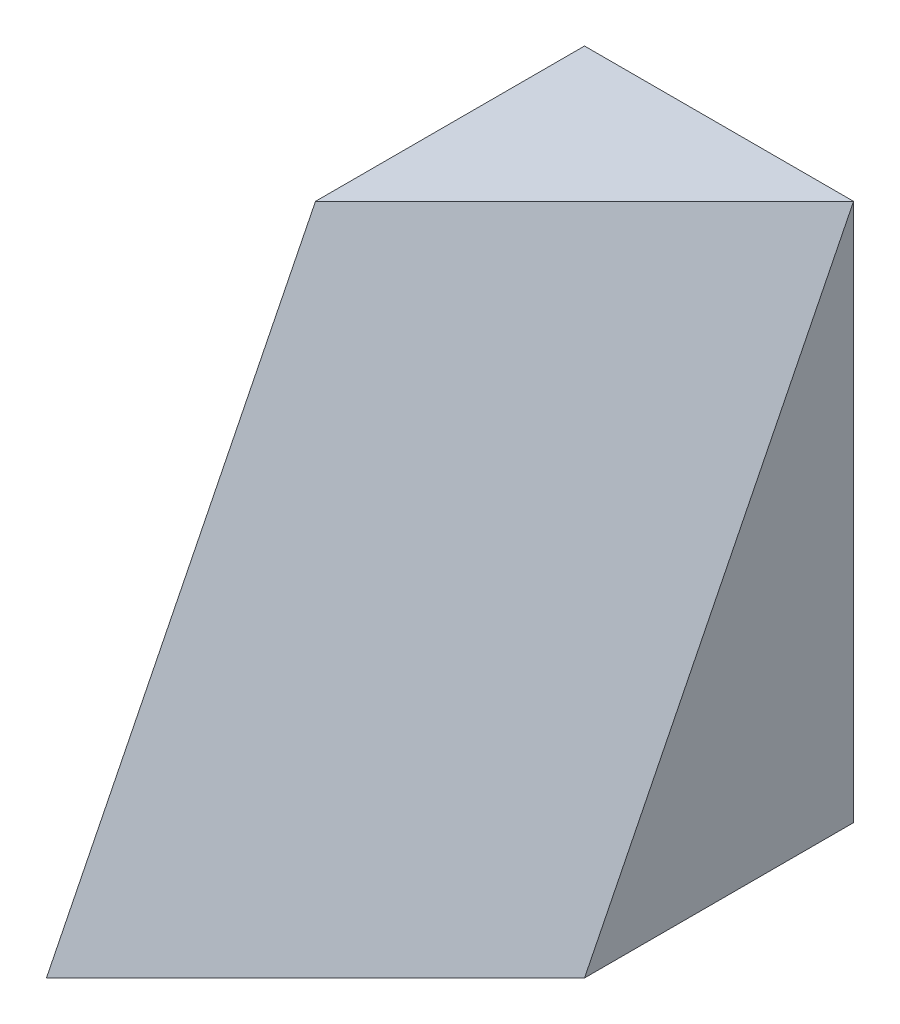
SolidWorks part; units mm, degrees
ref_plane "Front Plane" through (0, 0, 0) normal (0, 0, 1) x (1, 0, 0)
ref_plane "Top Plane" through (0, 0, 0) normal (0, 1, 0) x (1, 0, 0)
ref_plane "Right Plane" through (0, 0, 0) normal (1, 0, 0) x (0, 0, -1)
sketch "Sketch1" plane through (0, 0, 0) normal (0, 0, 1) x (1, 0, 0)
  line L1 (0, 0) -> (40, 0)
  line L2 (0, 0) -> (0, 40)
  line L3 (0, 40) -> (40, 40)
  line L4 (40, 0) -> (40, 40)
  dimension "D1" = 40
  dimension "D2" = 40
extrude "Boss-Extrude1" add sketch "Sketch1" along normal blind 40
sketch "Sketch2" plane through (0, 0, 40) normal (0, 0, 1) x (1, 0, 0)
  line L0 (0, 0) -> (20, 40)
  line L1 (40, 40) -> (0, 40) construction
  line L2 (20, 40) -> (0, 40)
  line L3 (0, 40) -> (0, 0)
extrude "Cut-Extrude1" cut sketch "Sketch2" against normal blind 40
sketch "Sketch3" plane through (0, 0, 0) normal (0, -1, 0) x (-1, 0, 0)
  line L0 (0, 0) -> (-20, -20)
  line L1 (-20, -20) -> (-20, -40)
  line L2 (0, -40) -> (-40, -40) construction
  line L3 (-20, -40) -> (0, -40)
  line L4 (0, -40) -> (0, 0)
  dimension "D1" = 20
  dimension "D2" = 20
extrude "Cut-Extrude2" cut sketch "Sketch3" against normal blind 40
ref_plane "Plane1" through (26.6667, 26.6667, 26.6667) normal (-0.5774, -0.5774, -0.5774) x (-0.8165, 0.4082, 0.4082)
sketch "Sketch12" plane through (20, 0, 0) normal (-1, 0, 0) x (0, 0, 1)
  line L0 (20, 40) -> (40, 0)
  line L1 (40, 0) -> (40, 40)
  line L2 (40, 40) -> (20, 40)
extrude "Cut-Extrude10" cut sketch "Sketch12" against normal blind 40
sketch "Sketch13" plane through (0, 0, 0) normal (0, -1, 0) x (1, 0, 0)
  line L0 (20, 40) -> (40, 20)
  line L1 (40, 40) -> (40, 0) construction
  line L2 (40, 20) -> (40, 40)
  line L3 (40, 40) -> (20, 40)
extrude "Cut-Extrude11" cut sketch "Sketch13" against normal blind 40
ref_plane "Plane4" through (0, 16, 32) normal (0, 0.4472, 0.8944) x (1, 0, 0)
ref_plane "Plane5" through (26.6667, 13.3333, 26.6667) normal (-0.6667, -0.3333, -0.6667) x (-0.7454, 0.2981, 0.5963)
sketch "Sketch14" plane through (26.6667, 13.3333, 26.6667) normal (-0.6667, -0.3333, -0.6667) x (-0.7454, 0.2981, 0.5963)
  line L0 (-17.8885, 35.7771) -> (-17.8885, -8.9443)
  line L1 (-17.8885, -8.9443) -> (8.9443, -17.8885)
  line L2 (8.9443, -17.8885) -> (8.9443, 26.8328)
  line L3 (8.9443, 26.8328) -> (-17.8885, 35.7771)
extrude "Cut-Extrude12" cut sketch "Sketch14" against normal blind 40
